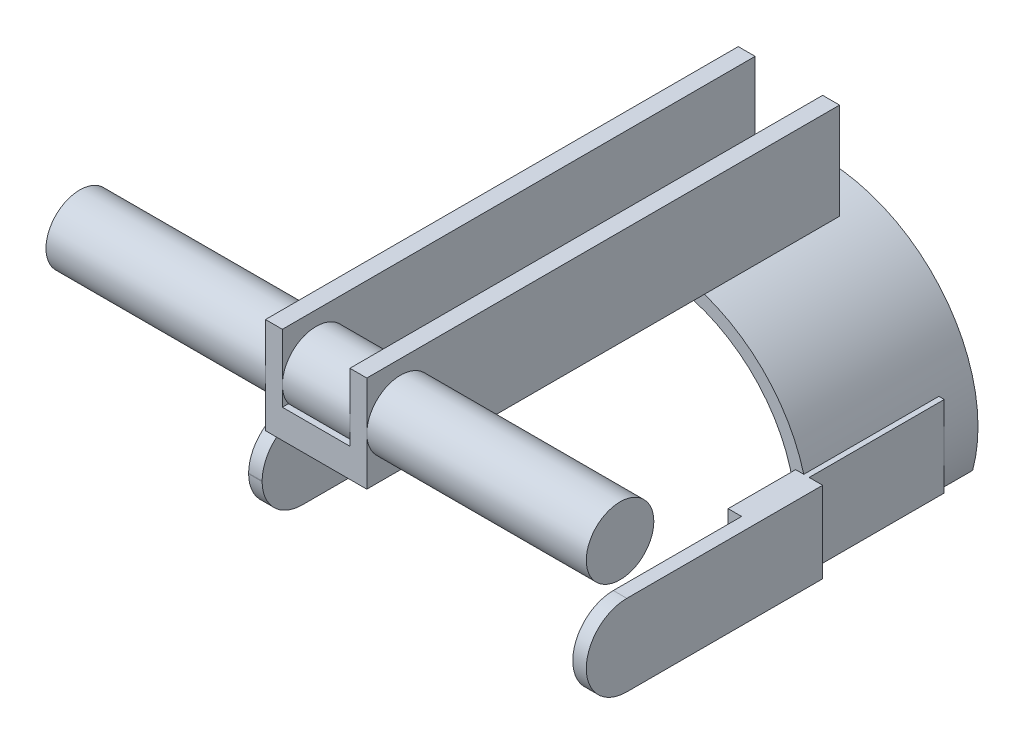
SolidWorks part; units mm, degrees
ref_plane "Front" through (0, 0, 0) normal (0, 0, 1) x (1, 0, 0)
ref_plane "Top" through (0, 0, 0) normal (0, 1, 0) x (1, 0, 0)
ref_plane "Right" through (0, 0, 0) normal (1, 0, 0) x (0, 0, -1)
sketch "草图2" plane through (0, 0, 0) normal (0, 0, 1) x (1, 0, 0)
  line L0 (-75.444, 0) -> (0, 0) construction
  line L1 (0, 0) -> (0, 80.5315) construction
  line L2 (-46, 0) -> (-42, 0)
  line L3 (42, 0) -> (46, 0)
  line L4 (20.6223, 42) -> (-21.3484, 42) construction
  line L5 (-15, 72) -> (-10, 72)
  line L6 (-15, 72) -> (-15, 43.4856)
  line L8 (15, 72) -> (15, 43.4856)
  line L9 (10, 72) -> (15, 72)
  line L11 (-10, 72) -> (-10, 52)
  line L12 (-10, 52) -> (10, 52)
  line L13 (10, 72) -> (10, 52)
  arc A0 (-46, 0) -> (-15, 43.4856) centre (0, 0) cw
  arc A1 (-42, 0) -> (42, 0) centre (0, 0) cw
  arc A2 (15, 43.4856) -> (46, 0) centre (0, 0) cw
  dimension "D1" = 30
  dimension "D2" = 15
  dimension "D3" = 20
  dimension "D4" = 30
  dimension "D5" = 10
  dimension "D6" = 20
extrude "凸台-拉伸1" add sketch "草图2" along normal blind 50
sketch "草图3" plane through (0, 0, 0) normal (0, 0, -1) x (-1, 0, 0)
  line L0 (0, 0) -> (-58.5553, 0) construction
  line L1 (-46, 12) -> (-42, 12)
  line L2 (-46, 12) -> (-46, -12)
  line L3 (-46, -12) -> (-42, -12)
  line L4 (-42, 12) -> (-42, -12)
  line L5 (46, 12) -> (42, 12)
  line L6 (46, 12) -> (46, -12)
  line L7 (46, -12) -> (42, -12)
  line L8 (42, 12) -> (42, -12)
  line L9 (0, 0) -> (0, 49.129) construction
  dimension "D1" = 4
  dimension "D2" = 46
  dimension "D3" = 24
  dimension "D4" = 12
  dimension "D5" = 4
  dimension "D6" = 24
  dimension "D7" = 12
  dimension "D8" = 46
extrude "凸台-拉伸2" add sketch "草图3" against normal blind 70
sketch "草图5" plane through (0, 0, 0) normal (0, 0, -1) x (-1, 0, 0)
  circle A0 centre (0, 0) radius 46
  circle A1 centre (0, 0) radius 80
extrude "切除-拉伸2" cut sketch "草图5" against normal blind 10
sketch "草图9" plane through (0, 0, 10) normal (0, 0, -1) x (-1, 0, 0)
  line L0 (-15, 72) -> (-15, 43.4856)
  line L1 (-15, 43.4856) -> (15, 43.4856)
  line L2 (15, 43.4856) -> (15, 72)
  line L3 (15, 72) -> (10, 72)
  line L4 (10, 72) -> (10, 52)
  line L5 (10, 52) -> (-10, 52)
  line L6 (-10, 52) -> (-10, 72)
  line L7 (-10, 72) -> (-15, 72)
extrude "凸台-拉伸4" add sketch "草图9" against normal blind 140
sketch "草图10" plane through (0, 0, 0) normal (1, 0, 0) x (0, 0, -1)
  line L0 (-150, 72) -> (-150, 43.4856) construction
  circle A0 centre (-140, 57.7428) radius 10
  dimension "D1" = 10
extrude "凸台-拉伸5" add sketch "草图10" along normal mid plane 160
sketch "草图12" plane through (0, -12, 0) normal (0, -1, 0) x (1, 0, 0)
  line L0 (-46, 70) -> (-46, 10) construction
  line L1 (-46, 49.9997) -> (-50, 49.9997)
  line L2 (-46, 49.9997) -> (-46, 119.9997)
  line L3 (-46, 119.9997) -> (-50, 119.9997)
  line L4 (-50, 49.9997) -> (-50, 119.9997)
  line L5 (46, 70) -> (46, 10) construction
  line L6 (46, 50) -> (50, 50)
  line L7 (46, 50) -> (46, 120)
  line L8 (46, 120) -> (50, 120)
  line L9 (50, 50) -> (50, 120)
  dimension "D1" = 4
  dimension "D2" = 70
  dimension "D3" = 4
  dimension "D4" = 70
extrude "凸台-拉伸6" add sketch "草图12" against normal blind 24
sketch "草图13" plane through (-50, 0, 0) normal (-1, 0, 0) x (0, 0, 1)
  line L1 (108, 12) -> (128.1969, 12)
  line L3 (108, -12) -> (128.1969, -12)
  line L4 (128.1969, 12) -> (128.1969, -12)
  arc A0 (108, -12) -> (108, 12) centre (108, 0) ccw
extrude "切除-拉伸3" cut sketch "草图13" against normal through all
